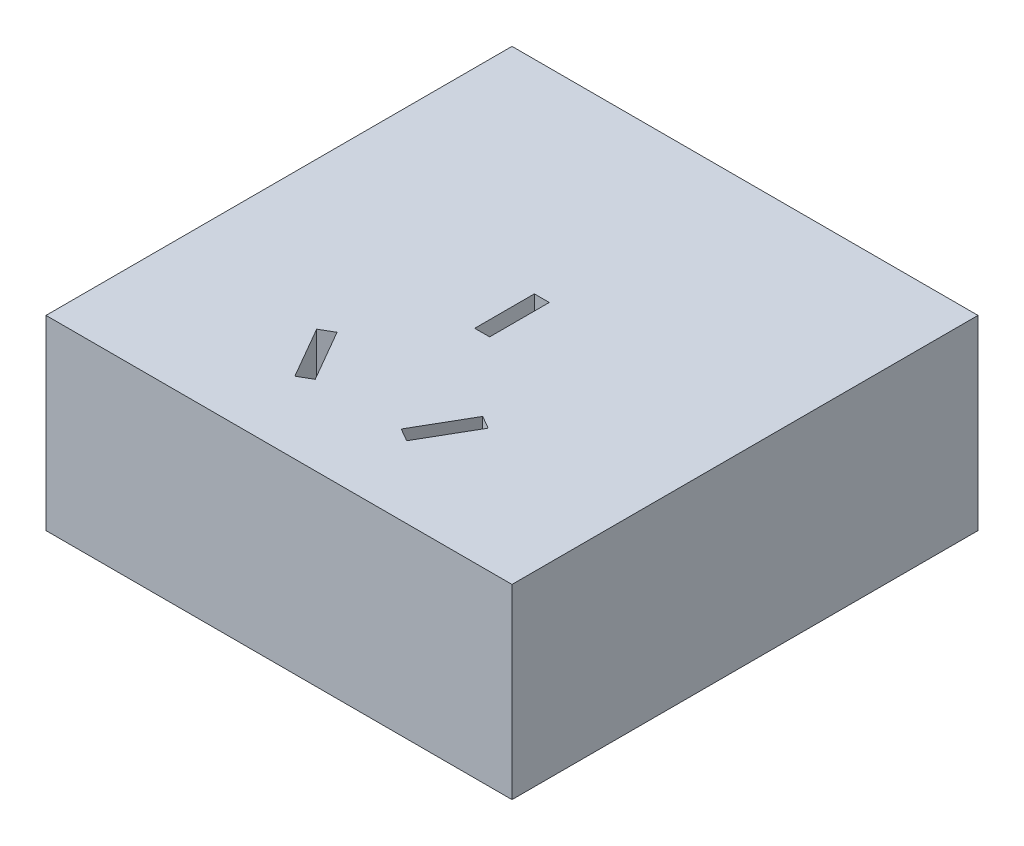
SolidWorks part; units mm, degrees
ref_plane "Спереди" through (0, 0, 0) normal (0, 0, 1) x (1, 0, 0)
ref_plane "Сверху" through (0, 0, 0) normal (0, 1, 0) x (1, 0, 0)
ref_plane "Справа" through (0, 0, 0) normal (1, 0, 0) x (0, 0, -1)
sketch "Эскиз1" plane through (0, 0, 0) normal (0, 1, 0) x (1, 0, 0)
  line L1 (-25, 25) -> (25, 25)
  line L2 (-25, 25) -> (-25, -25)
  line L3 (-25, -25) -> (25, -25)
  line L4 (25, 25) -> (25, -25)
  line L5 (-25, 25) -> (25, -25) construction
  line L6 (-25, -25) -> (25, 25) construction
  point P0 (0, 0)
extrude "Бобышка-Вытянуть1" add sketch "Эскиз1" along normal blind 20
sketch "Эскиз2" plane through (0, 20, 0) normal (0, 1, 0) x (1, 0, 0)
  line L0 (-0.8, 3.2) -> (0.8, 3.2)
  line L1 (0.8, 3.2) -> (0.8, -3.2)
  line L2 (0.8, -3.2) -> (0, -3.2)
  line L3 (4.6144, -16.5) -> (7.8144, -10.9574)
  line L4 (7.8144, -10.9574) -> (9.2, -11.7574)
  line L5 (9.2, -11.7574) -> (6, -17.3)
  line L6 (6, -17.3) -> (4.6144, -16.5)
  line L7 (0, 19.2396) -> (0, -26.2315) construction
  line L8 (-6, -17.3) -> (-4.6144, -16.5)
  line L9 (-9.2, -11.7574) -> (-6, -17.3)
  line L10 (-7.8144, -10.9574) -> (-9.2, -11.7574)
  line L11 (-4.6144, -16.5) -> (-7.8144, -10.9574)
  line L12 (-0.8, -3.2) -> (0, -3.2)
  line L13 (-0.8, 3.2) -> (-0.8, -3.2)
  point P0 (0, -3.1984)
  point P18 (0, 3.2)
extrude "Вырез-Вытянуть1" cut sketch "Эскиз2" against normal blind 20
